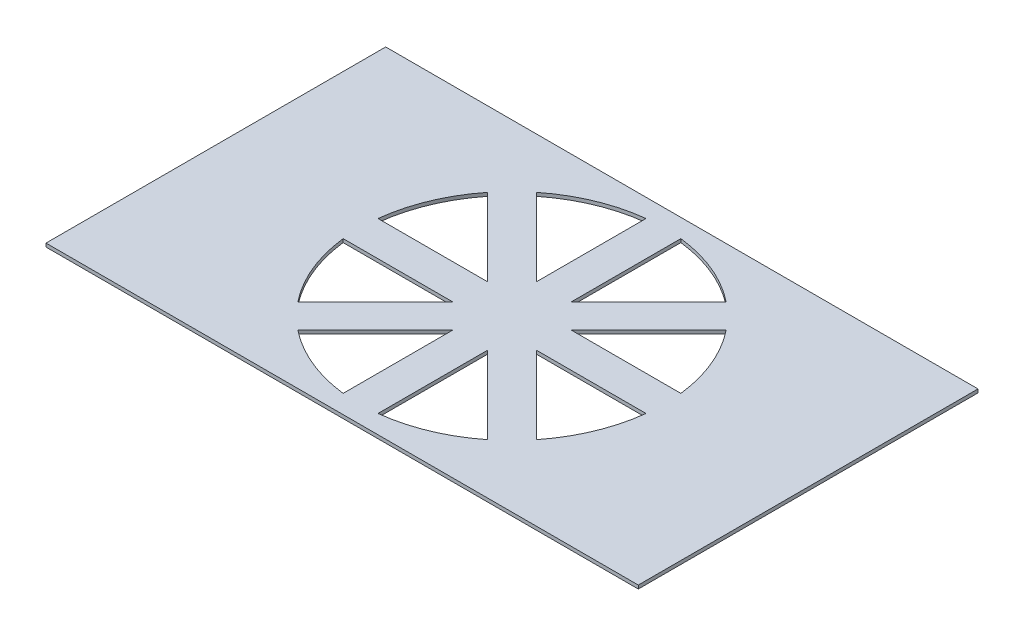
SolidWorks part; units mm, degrees
ref_plane "Ebene vorne" through (0, 0, 0) normal (0, 0, 1) x (1, 0, 0)
ref_plane "Ebene oben" through (0, 0, 0) normal (0, 1, 0) x (1, 0, 0)
ref_plane "Ebene rechts" through (0, 0, 0) normal (1, 0, 0) x (0, 0, -1)
sketch "Sketch1" plane through (0, 0, 0) normal (0, 1, 0) x (1, 0, 0)
  line L0 (0, 39) -> (27.3678, 23.3037) construction
  line L1 (0, 0) -> (68, 0)
  line L2 (0, 0) -> (0, 39)
  line L3 (0, 39) -> (68, 39)
  line L4 (68, 0) -> (68, 39)
  line L5 (44.8791, 33.2075) -> (36, 24.3284)
  line L6 (51.3853, 17.5) -> (38.8284, 17.5)
  line L8 (51.3853, 21.5) -> (38.8284, 21.5)
  line L10 (32, 14.6716) -> (23.1209, 5.7925)
  line L12 (32, 39) -> (36, 39)
  line L13 (32, 36.8853) -> (32, 24.3284)
  line L14 (32, 0) -> (36, 0)
  line L15 (36, 36.8853) -> (36, 24.3284)
  line L16 (29.1716, 17.5) -> (16.6147, 17.5)
  line L20 (47.7075, 30.3791) -> (38.8284, 21.5)
  line L21 (29.1716, 17.5) -> (20.2925, 8.6209)
  line L23 (47.7075, 8.6209) -> (38.8284, 17.5)
  line L26 (44.8791, 5.7925) -> (36, 14.6716)
  line L28 (32, 14.6716) -> (32, 2.1147)
  line L29 (36, 14.6716) -> (36, 2.1147)
  line L31 (40.6322, 15.6963) -> (68, 0) construction
  line L47 (29.1716, 21.5) -> (20.2925, 30.3791)
  line L49 (29.1716, 21.5) -> (16.6147, 21.5)
  line L52 (32, 24.3284) -> (23.1209, 33.2075)
  arc A0 (16.6147, 17.5) -> (20.2925, 8.6209) centre (34, 19.5) ccw
  arc A1 (23.1209, 5.7925) -> (32, 2.1147) centre (34, 19.5) ccw
  arc A2 (36, 2.1147) -> (44.8791, 5.7925) centre (34, 19.5) ccw
  arc A3 (47.7075, 8.6209) -> (51.3853, 17.5) centre (34, 19.5) ccw
  arc A4 (51.3853, 21.5) -> (47.7075, 30.3791) centre (34, 19.5) ccw
  arc A5 (44.8791, 33.2075) -> (36, 36.8853) centre (34, 19.5) ccw
  arc A6 (32, 36.8853) -> (23.1209, 33.2075) centre (34, 19.5) ccw
  arc A7 (20.2925, 30.3791) -> (16.6147, 21.5) centre (34, 19.5) ccw
  dimension "D3" = 35
  dimension "D1" = 68
  dimension "D2" = 39
  dimension "D5" = 4
  dimension "D6" = 45
  dimension "D8" = 45
extrude "Boss-Extrude1" add sketch "Sketch1" along normal blind 0.4 contours L1 L4 L3 L2 A7 L47 L49 A6 L13 L52 A5 L5 L15 A4 L8 L20 A3 L23 L6 A2 L29 L26 A1 L10 L28 A0 L16 L21
